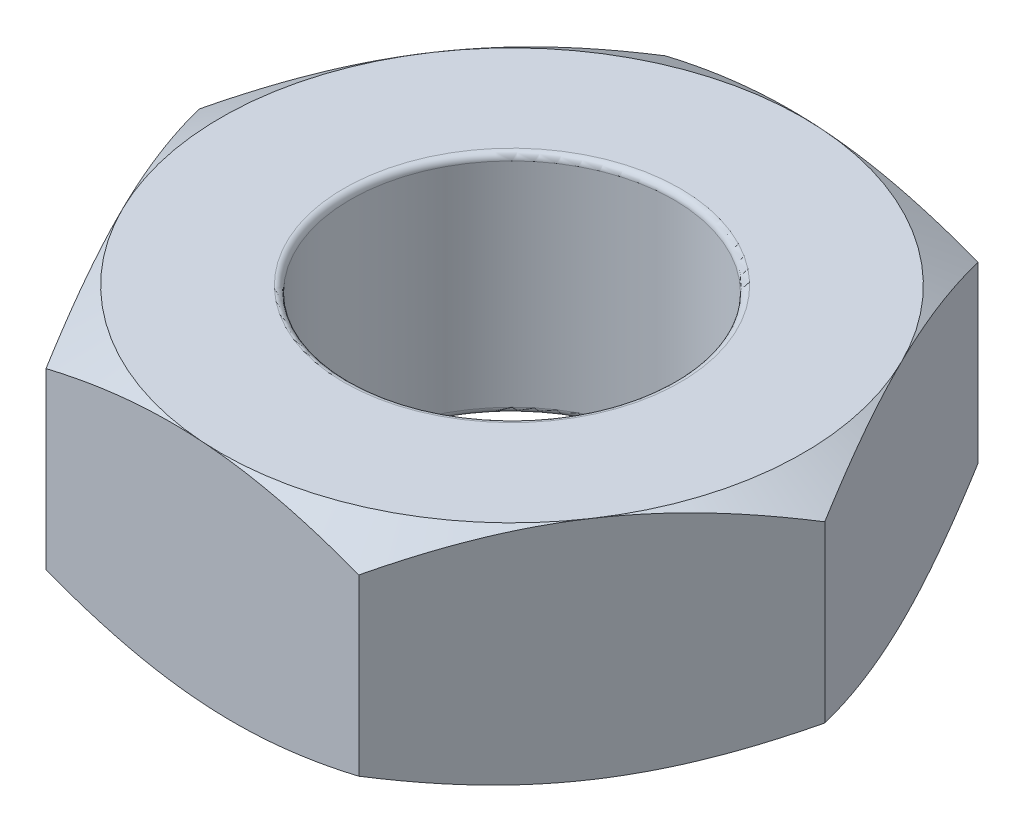
SolidWorks part; units mm, degrees
ref_plane "Front Plane" through (0, 0, 0) normal (0, 0, 1) x (1, 0, 0)
ref_plane "Top Plane" through (0, 0, 0) normal (0, 1, 0) x (1, 0, 0)
ref_plane "Right Plane" through (0, 0, 0) normal (1, 0, 0) x (0, 0, -1)
sketch "Sketch1" plane through (0, 0, 0) normal (0, 1, 0) x (1, 0, 0)
  line L1 (-2.5923, 0.1731) -> (-1.4461, -2.1585)
  line L2 (-1.4461, -2.1585) -> (1.1463, -2.3315)
  line L3 (1.1463, -2.3315) -> (2.5923, -0.1731)
  line L4 (2.5923, -0.1731) -> (1.4461, 2.1585)
  line L5 (1.4461, 2.1585) -> (-1.1463, 2.3315)
  line L6 (-1.1463, 2.3315) -> (-2.5923, 0.1731)
  circle A0 centre (0, 0) radius 2.25 construction
  circle A1 centre (0, 0) radius 1.25
  dimension "D1" = 4.5
  dimension "D2" = 2.5
extrude "Boss-Extrude1" add sketch "Sketch1" along normal blind 1.75
sketch "Sketch2" plane through (0, 1.75, 0) normal (0, 1, 0) x (1, 0, 0)
  circle A0 centre (0, 0) radius 2.25 construction
  circle A1 centre (0, 0) radius 2.25
extrude "Cut-Extrude1" cut sketch "Sketch2" against normal blind 2 draft 60 flip side to cut
sketch "Sketch3" plane through (0, 0, 0) normal (0, -1, 0) x (1, 0, 0)
  circle A0 centre (0, 0) radius 2.25 construction
  circle A1 centre (0, 0) radius 2.25
extrude "Cut-Extrude2" cut sketch "Sketch3" against normal blind 2 draft 60 flip side to cut
fillet "Fillet1" radius 0.05 2 edges at (0, 0, 1.25) (0, 1.75, 1.25)
